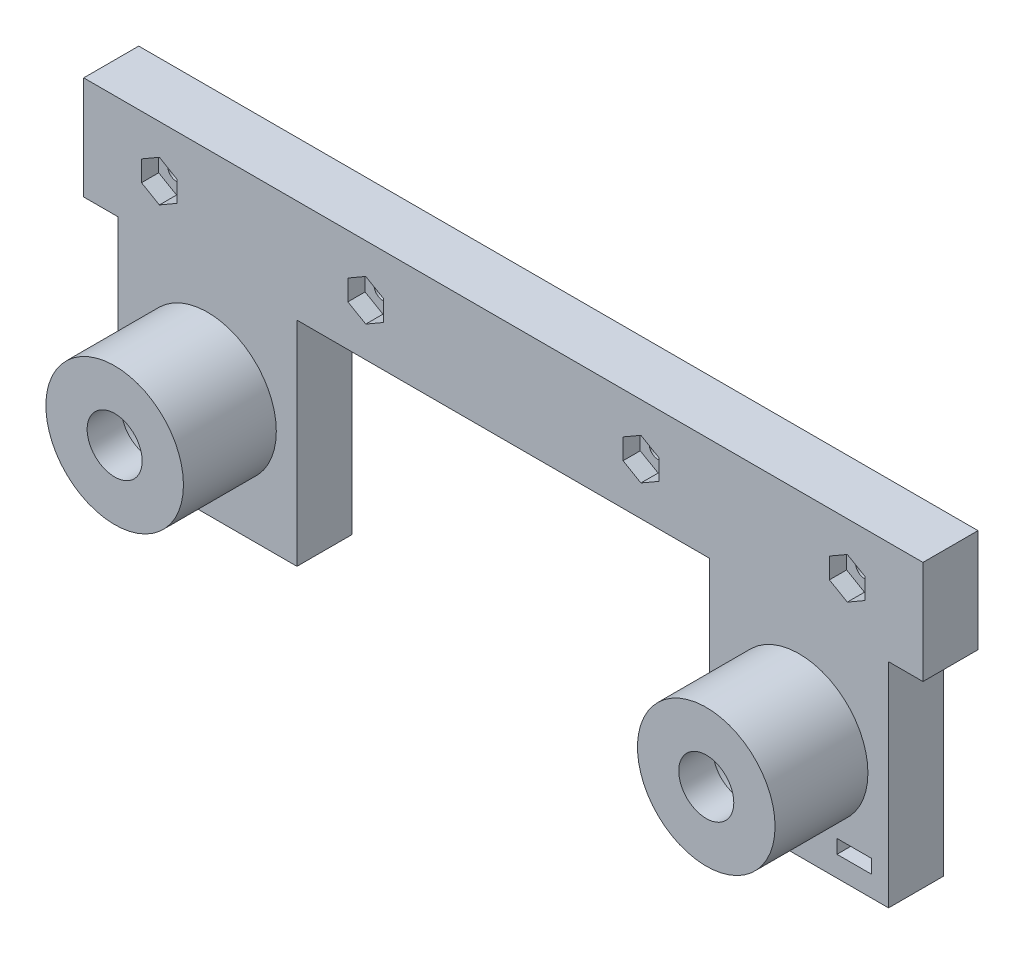
SolidWorks part; units mm, degrees
ref_plane "Front Plane" through (0, 0, 0) normal (0, 0, 1) x (1, 0, 0)
ref_plane "Top Plane" through (0, 0, 0) normal (0, 1, 0) x (1, 0, 0)
ref_plane "Right Plane" through (0, 0, 0) normal (1, 0, 0) x (0, 0, -1)
sketch "Sketch1" plane through (0, 0, 0) normal (0, 0, 1) x (1, 0, 0)
  line L1 (-61, 7.5) -> (61, 7.5)
  line L2 (-61, 7.5) -> (-61, -7.5)
  line L3 (-61, -7.5) -> (61, -7.5)
  line L4 (61, 7.5) -> (61, -7.5)
  line L5 (-61, 7.5) -> (61, -7.5) construction
  line L6 (-61, -7.5) -> (61, 7.5) construction
  point P0 (0, 0)
  dimension "D1" = 15
  dimension "D2" = 122
extrude "Boss-Extrude1" add sketch "Sketch1" along normal blind 8
sketch "Sketch2" plane through (0, 0, 8) normal (0, 0, 1) x (1, 0, 0)
  circle A0 centre (-20, 0) radius 1.3
  circle A1 centre (20, 0) radius 1.3
  circle A2 centre (-50, 0) radius 1.3
  circle A3 centre (50, 0) radius 1.3
  dimension "D3" = 30
  dimension "D4" = 30
  dimension "D5" = 2.6
  dimension "D1" = 20
  dimension "D2" = 20
extrude "Cut-Extrude1" cut sketch "Sketch2" against normal through all both and the other way through all
sketch "Sketch4" plane through (0, 0, 8) normal (0, 0, 1) x (1, 0, 0)
  line L1 (-50, 3) -> (-52.5981, 1.5)
  line L2 (-52.5981, 1.5) -> (-52.5981, -1.5)
  line L3 (-52.5981, -1.5) -> (-50, -3)
  line L4 (-50, -3) -> (-47.4019, -1.5)
  line L5 (-47.4019, -1.5) -> (-47.4019, 1.5)
  line L6 (-47.4019, 1.5) -> (-50, 3)
  line L7 (-20, 3) -> (-22.5981, 1.5)
  line L8 (-22.5981, 1.5) -> (-22.5981, -1.5)
  line L9 (-22.5981, -1.5) -> (-20, -3)
  line L10 (-20, -3) -> (-17.4019, -1.5)
  line L11 (-17.4019, -1.5) -> (-17.4019, 1.5)
  line L12 (-17.4019, 1.5) -> (-20, 3)
  line L13 (20, 3) -> (17.4019, 1.5)
  line L14 (17.4019, 1.5) -> (17.4019, -1.5)
  line L15 (17.4019, -1.5) -> (20, -3)
  line L16 (20, -3) -> (22.5981, -1.5)
  line L17 (22.5981, -1.5) -> (22.5981, 1.5)
  line L18 (22.5981, 1.5) -> (20, 3)
  line L19 (50, 3) -> (47.4019, 1.5)
  line L20 (47.4019, 1.5) -> (47.4019, -1.5)
  line L21 (47.4019, -1.5) -> (50, -3)
  line L22 (50, -3) -> (52.5981, -1.5)
  line L23 (52.5981, -1.5) -> (52.5981, 1.5)
  line L24 (52.5981, 1.5) -> (50, 3)
  circle A0 centre (-50, 0) radius 2.5981 construction
  circle A1 centre (-20, 0) radius 2.5981 construction
  circle A2 centre (20, 0) radius 2.5981 construction
  circle A3 centre (50, 0) radius 2.5981 construction
  dimension "D1" = 6
extrude "Cut-Extrude3" cut sketch "Sketch4" against normal blind 2.5
sketch "Sketch5" plane through (0, 0, 0) normal (0, 0, 1) x (1, 0, 0)
  line L0 (-61, -7.5) -> (61, -7.5) construction
  line L1 (-56, -23) -> (-56, -7.5)
  line L2 (-56, -7.5) -> (-30, -7.5)
  line L3 (-30, -7.5) -> (-30, -23)
  line L4 (30, -23) -> (30, -7.5)
  line L5 (30, -7.5) -> (56, -7.5)
  line L6 (56, -7.5) -> (56, -23)
  line L7 (56, -23) -> (56, -38.5)
  line L8 (56, -38.5) -> (30, -38.5)
  line L9 (30, -38.5) -> (30, -23)
  line L10 (-30, -23) -> (-30, -38.5)
  line L11 (-30, -38.5) -> (-56, -38.5)
  line L12 (-56, -38.5) -> (-56, -23)
  line L13 (-61, -7.5) -> (61, -7.5) construction
  line L14 (-32, -23) -> (-32, -12.9666) construction
  line L15 (32, -23) -> (32, -12.9666) construction
  line L16 (-43, -38.5) -> (-43, -7.5) construction
  circle A0 centre (-43, -23) radius 7.5
  circle A1 centre (43, -23) radius 7.5
  circle A2 centre (-43, -23) radius 11
  circle A3 centre (43, -23) radius 11
  dimension "D1" = 15
  dimension "D4" = 22
  dimension "D2" = 30
  dimension "D3" = 30
  dimension "D5" = 23
  dimension "D6" = 31
  dimension "D7" = 26
  dimension "D8" = 26
  dimension "D9" = 43
extrude "Boss-Extrude2" add sketch "Sketch5" along normal blind 8 contours A2 L2 A0 | A2 L2 L1 | L2 A2 | A2 L3 L2 | A3 L6 L5 | A3 L5 A1 | A3 L5 L4 | L5 A3
sketch "Sketch6" plane through (0, 0, 8) normal (0, 0, 1) x (1, 0, 0)
  circle A0 centre (-43, -23) radius 7.5
  circle A1 centre (-43, -23) radius 10
  circle A2 centre (43, -23) radius 7.5
  circle A3 centre (43, -23) radius 10
  circle A4 centre (-43, -23) radius 7.5 construction
  circle A5 centre (43, -23) radius 7.5 construction
  dimension "D1" = 20
extrude "Boss-Extrude3" add sketch "Sketch6" along normal blind 8.5
sketch "Sketch7" plane through (0, 0, 16.5) normal (0, 0, 1) x (1, 0, 0)
  circle A0 centre (-43, -23) radius 4
  circle A1 centre (-43, -23) radius 10
  circle A2 centre (43, -23) radius 4
  circle A3 centre (43, -23) radius 10
  circle A4 centre (43, -23) radius 10 construction
  circle A5 centre (-43, -23) radius 10 construction
  dimension "D1" = 8
extrude "Boss-Extrude4" add sketch "Sketch7" along normal blind 5
sketch "Sketch8" plane through (0, -38.5, 0) normal (0, -1, 0) x (1, 0, 0)
  line L0 (-56, 4) -> (56, 4) construction
  line L1 (-56, 8) -> (-56, 0) construction
  line L2 (56, 8) -> (56, 0) construction
  line L3 (-56, 8) -> (-56, 0) construction
  circle A0 centre (51, 4) radius 1.3
  circle A1 centre (-51, 4) radius 1.3
  dimension "D3" = 2.6
  dimension "D2" = 5
  dimension "D1" = 5
extrude "Cut-Extrude4" cut sketch "Sketch8" against normal blind 5
sketch "Sketch9" plane through (0, 0, 8) normal (0, 0, 1) x (1, 0, 0)
  line L0 (-56, -38.5) -> (-56, -7.5) construction
  line L5 (-53.5, -33.5) -> (-48.5, -33.5)
  line L6 (-53.5, -33.5) -> (-53.5, -35.5)
  line L7 (48.5, -33.5) -> (53.5, -33.5)
  line L8 (48.5, -33.5) -> (48.5, -35.5)
  line L9 (48.5, -35.5) -> (53.5, -35.5)
  line L10 (53.5, -33.5) -> (53.5, -35.5)
  line L11 (48.5, -33.5) -> (53.5, -35.5) construction
  line L12 (48.5, -35.5) -> (53.5, -33.5) construction
  line L14 (56, -7.5) -> (56, -38.5) construction
  line L16 (-53.5, -35.5) -> (-48.5, -35.5)
  line L17 (-48.5, -33.5) -> (-48.5, -35.5)
  line L18 (-53.5, -33.5) -> (-48.5, -35.5) construction
  line L19 (-53.5, -35.5) -> (-48.5, -33.5) construction
  line L20 (-30, -38.5) -> (-56, -38.5) construction
  point P0 (-51, -34.5)
  point P5 (51, -34.5)
  dimension "D1" = 2
  dimension "D2" = 5
  dimension "D3" = 5
  dimension "D4" = 3
  dimension "D5" = 5
extrude "Cut-Extrude5" cut sketch "Sketch9" against normal through all both and the other way through all
